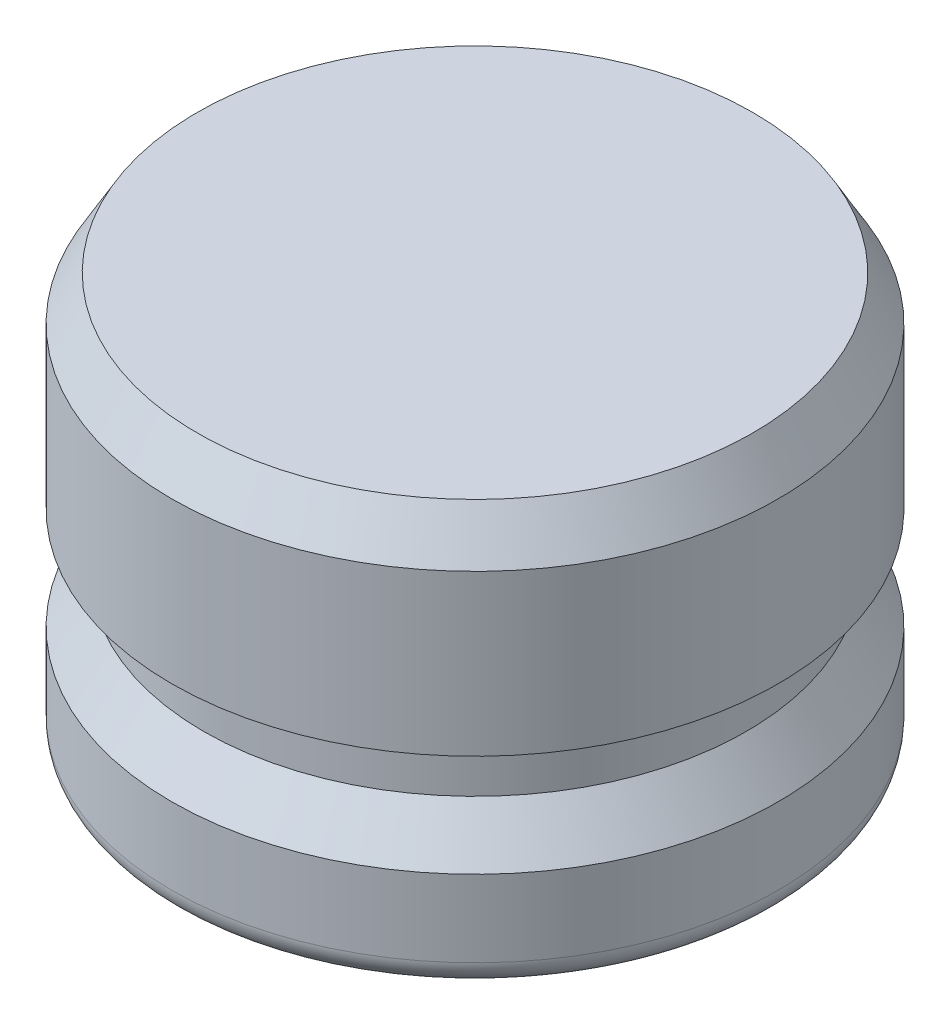
SolidWorks part; units mm, degrees
ref_plane "Front Plane" through (0, 0, 0) normal (0, 0, 1) x (1, 0, 0)
ref_plane "Top Plane" through (0, 0, 0) normal (0, 1, 0) x (1, 0, 0)
ref_plane "Right Plane" through (0, 0, 0) normal (1, 0, 0) x (0, 0, -1)
sketch "Sketch1" plane through (0, 0, 0) normal (0, 0, 1) x (1, 0, 0)
  line L0 (0, 0) -> (0, 12.7) construction
  line L1 (0, 0) -> (-9.4234, 0)
  line L2 (-9.4234, 0) -> (-9.4234, 3.175)
  line L4 (-8.4328, 4.572) -> (-8.4328, 6.35)
  line L5 (-8.4328, 6.35) -> (-9.4234, 6.35)
  line L6 (-9.4234, 6.35) -> (-9.4234, 12.7)
  line L7 (-9.4234, 12.7) -> (0, 12.7)
  line L8 (-9.525, 16.6801) -> (-9.525, -9.6051) construction
  line L9 (0, 0) -> (0, 12.7)
  line L10 (-8.4328, 4.572) -> (-9.4234, 3.175)
  dimension "D1" = 12.7
  dimension "D2" = 9.4234
  dimension "D3" = 1.778
  dimension "D4" = 3.175
  dimension "D5" = 9.525
  dimension "D6" = 8.4328
  dimension "D7" = 6.35
revolve "Revolve1" add sketch "Sketch1" angle 360 about L9
fillet "Fillet1" radius 0.7937 1 edges at (0, 0, -9.4234)
chamfer "Chamfer1" distance 0.7937 angle 60 1 edges at (0, 12.7, -9.4234)
